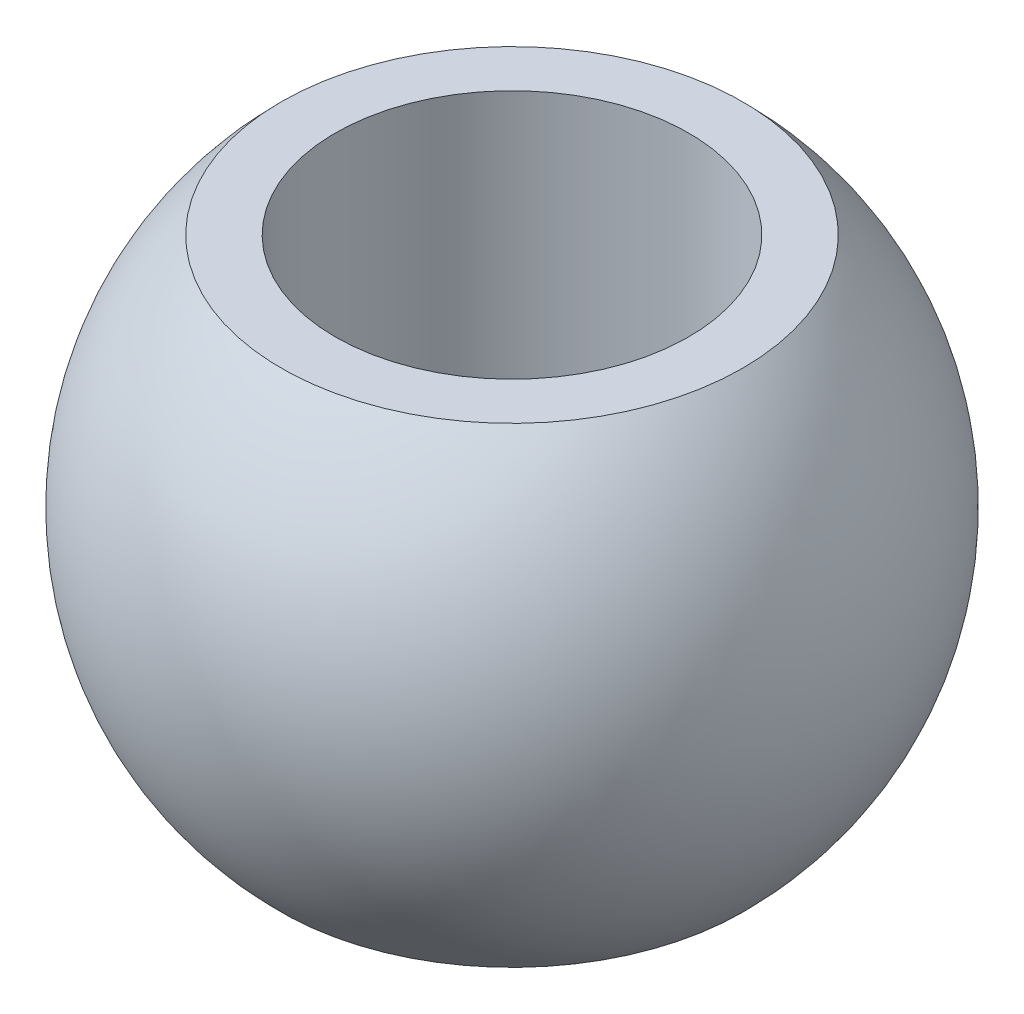
SolidWorks part; units mm, degrees
ref_plane "Front Plane" through (0, 0, 0) normal (0, 0, 1) x (1, 0, 0)
ref_plane "Top Plane" through (0, 0, 0) normal (0, 1, 0) x (1, 0, 0)
ref_plane "Right Plane" through (0, 0, 0) normal (1, 0, 0) x (0, 0, -1)
sketch "Sketch1" plane through (0, 0, 0) normal (0, 0, 1) x (1, 0, 0)
  line L0 (0, -9.3513) -> (0, 6.5237)
  line L5 (4, -9.3513) -> (4, 6.5237)
  line L6 (4, 6.5237) -> (9.6435, 6.5237)
  line L7 (4, 6.5237) -> (4, 4.9362)
  line L8 (4, 4.9362) -> (9.6435, 4.9362)
  line L9 (9.6435, 6.5237) -> (9.6435, 4.9362)
  line L10 (4, -9.3513) -> (9.525, -9.3513)
  line L11 (4, -9.3513) -> (4, -7.7638)
  line L12 (4, -7.7638) -> (9.525, -7.7638)
  line L13 (9.525, -9.3513) -> (9.525, -7.7638)
  arc A0 (4, -9.3513) -> (4, 6.5237) centre (0, -1.4138) ccw
  point P4 (0, 0)
  point P8 (0, -1.4138)
  dimension "D1" = 1.5875
  dimension "D3" = 8.8884
  dimension "D2" = 1.5875
  dimension "D4" = 15.875
  dimension "D5" = 15.875
  dimension "D6" = 4
revolve "Revolve1" add sketch "Sketch1" angle 360 about L0
sketch "Sketch2" plane through (0, 4.9362, 0) normal (0, 1, 0) x (1, 0, 0)
  circle A0 centre (0, 0) radius 4.7625
extrude "Cut-Extrude1" cut sketch "Sketch2" against normal through all
